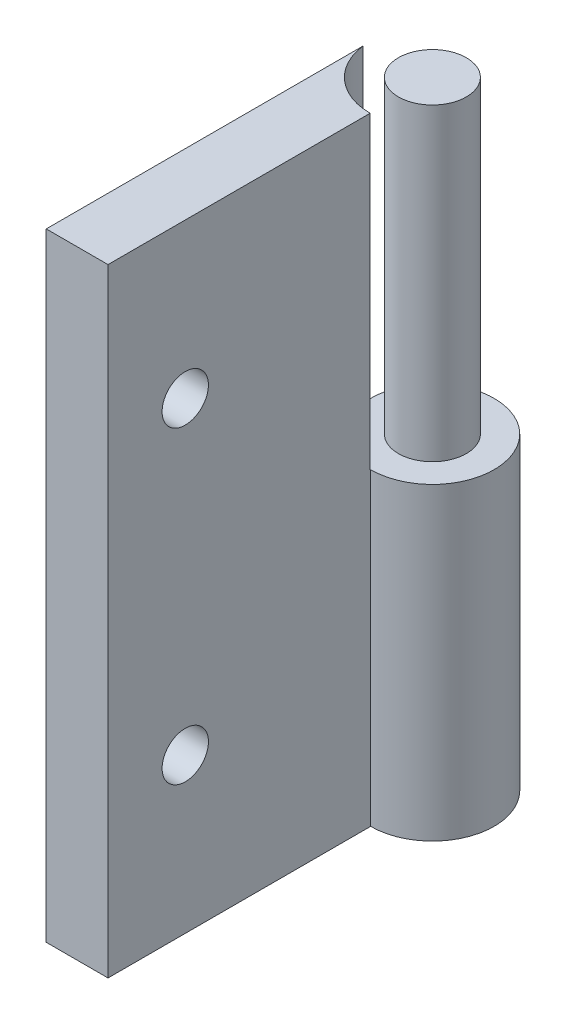
SolidWorks part; units mm, degrees
ref_plane "Front Plane" through (0, 0, 0) normal (0, 0, 1) x (1, 0, 0)
ref_plane "Top Plane" through (0, 0, 0) normal (0, 1, 0) x (1, 0, 0)
ref_plane "Right Plane" through (0, 0, 0) normal (1, 0, 0) x (0, 0, -1)
sketch "Sketch1" plane through (0, 0, 0) normal (0, 0, 1) x (1, 0, 0)
  line L0 (0, 0) -> (0, 40)
extrude "Extrude-Thin2" add sketch "Sketch1" along normal blind 21 thin
sketch "Sketch4" plane through (0, 40, 0) normal (0, 1, 0) x (1, 0, 0)
  circle A0 centre (4, 0) radius 4
sweep "Sweep3" add profiles "Sketch4" path edge at (4, 20, 0)
sketch "Sketch12" plane through (0, 40, 0) normal (0, 1, 0) x (1, 0, 0)
  circle A0 centre (4, 0) radius 4.035
  circle A1 centre (4, 0) radius 2.2
sketch "Sketch15" plane through (0, 40, 0) normal (0, 1, 0) x (1, 0, 0)
  circle A0 centre (4, 0) radius 2.2
  circle A2 centre (4, 0) radius 4.03
extrude "Cut-Extrude14" cut sketch "Sketch15" against normal blind 20
sketch "Sketch13" plane through (4, 0, 0) normal (1, 0, 0) x (0, 0, -1)
  line L0 (-21, 40) -> (-4.03, 40) construction
  line L2 (-21, 0) -> (-4, 0) construction
  circle A1 centre (-16, 30) radius 1.5
  circle A2 centre (-16, 10) radius 1.5
  dimension "D1" = 10
  dimension "D2" = 10
  dimension "D3" = 16
extrude "Cut-Extrude10" cut sketch "Sketch13" against normal through all
